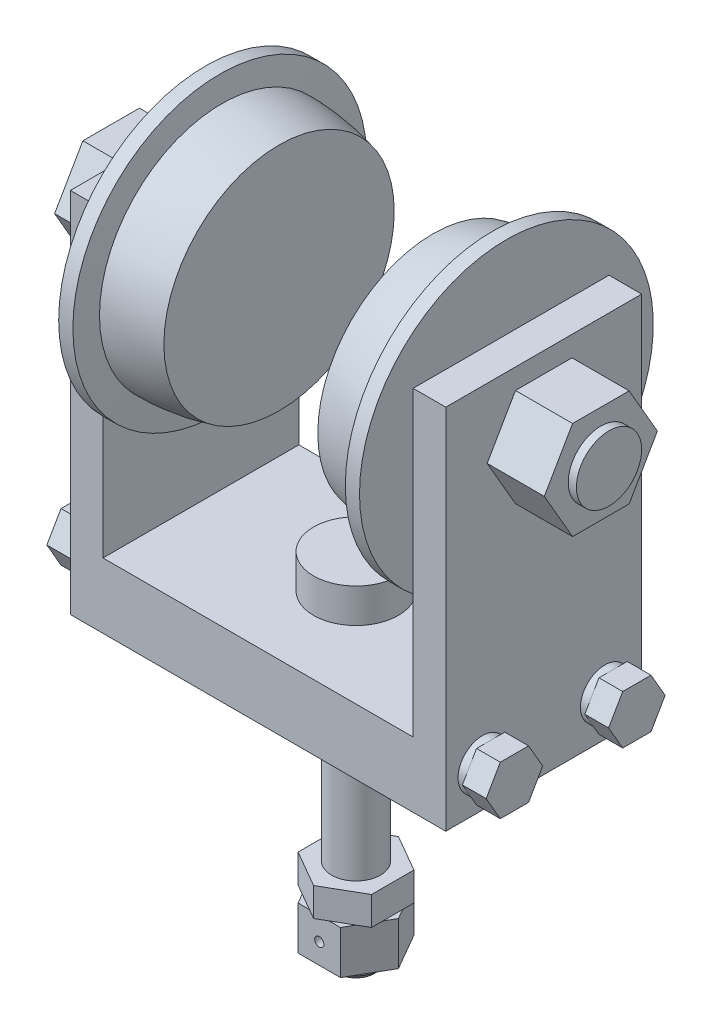
SolidWorks part; units mm, degrees
ref_plane "Front" through (0, 0, 0) normal (0, 0, 1) x (1, 0, 0)
ref_plane "Top" through (0, 0, 0) normal (0, 1, 0) x (1, 0, 0)
ref_plane "Right" through (0, 0, 0) normal (1, 0, 0) x (0, 0, -1)
ref_plane "Z PLANE" through (0, 0, 0) normal (0, 0, 1) x (1, 0, 0)
ref_plane "YOKE BOTTOM" through (0, 0, 0) normal (0, 1, 0) x (-1, 0, 0)
ref_plane "X PLANE" through (0, 0, 0) normal (1, 0, 0) x (0, 0, -1)
sketch "YOKE CROSS SECTION" plane through (0, 0, 0) normal (1, 0, 0) x (0, 0, -1)
  line L0 (0, 0) -> (0, 57.0916) construction
  line L1 (0, 72.125) -> (0, -72.125) construction
  line L2 (-38.1, 0) -> (38.1, 0)
  line L3 (69.1602, 0) -> (-69.1602, 0) construction
  line L4 (38.1, 0) -> (38.1, 25.4)
  line L5 (-38.1, 0) -> (-38.1, 25.4)
  line L6 (38.1, 25.4) -> (-38.1, 25.4)
  point P12 (0, 25.4)
  dimension "D1" = 25.4
  dimension "D2" = 76.2
ref_plane "1/2 YOKE LENGTH (A)" through (60.325, 0, 0) normal (1, 0, 0) x (0, 0, -1)
extrude "YOKE" add sketch "YOKE CROSS SECTION" along normal up to surface (60.325 mm away) up to plane "1/2 YOKE LENGTH (A)"
sketch "SIDEPLATE PROFILE" plane through (60.325, 0, 0) normal (1, 0, 0) x (0, 0, -1)
  line L0 (0, 0) -> (0, 74.7424) construction
  line L1 (0, 72.125) -> (0, -72.125) construction
  line L2 (-38.1, 0) -> (38.1, 0)
  line L3 (38.1, 0) -> (38.1, 142.875)
  line L4 (-38.1, 0) -> (-38.1, 142.875)
  line L5 (38.1, 142.875) -> (-38.1, 142.875)
  point P11 (0, 142.875)
  dimension "D1" = 142.875
ref_plane "WHEEL HEIGHT" through (0, 115.8875, 0) normal (0, 1, 0) x (-1, 0, 0)
ref_plane "SCREW LOCATION X" through (0, 0, 23.8125) normal (0, 0, 1) x (1, 0, 0)
ref_plane "SCREW LOCATION Y" through (0, 15.5632, 0) normal (0, 1, 0) x (-1, 0, 0)
extrude "SIDEPLATE" add sketch "SIDEPLATE PROFILE" along normal blind 12.7
sketch "WHEEL PIN NUT PROFILE" plane through (73.025, 0, 0) normal (1, 0, 0) x (0, 0, -1)
  line L0 (0, 72.125) -> (0, -72.125) construction
  line L1 (21.997, 115.8875) -> (10.9985, 134.9375)
  line L2 (10.9985, 134.9375) -> (-10.9985, 134.9375)
  line L3 (-10.9985, 134.9375) -> (-21.997, 115.8875)
  line L4 (-21.997, 115.8875) -> (-10.9985, 96.8375)
  line L5 (-10.9985, 96.8375) -> (10.9985, 96.8375)
  line L6 (10.9985, 96.8375) -> (21.997, 115.8875)
  line L7 (69.1602, 115.8875) -> (-69.1602, 115.8875) construction
  circle A0 centre (0, 115.8875) radius 19.05 construction
  dimension "D1" = 38.1
extrude "WHEEL PIN NUT" add sketch "WHEEL PIN NUT PROFILE" along normal blind 22.225
sketch "WHEEL PIN PROJECTION PROFILE" plane through (95.25, 0, 0) normal (1, 0, 0) x (0, 0, -1)
  line L0 (0, 72.125) -> (0, -72.125) construction
  line L1 (69.1602, 115.8875) -> (-69.1602, 115.8875) construction
  circle A0 centre (0, 115.8875) radius 12.7
  dimension "D1" = 25.4
extrude "WHEEL PIN PROJECTION" add sketch "WHEEL PIN PROJECTION PROFILE" along normal blind 3.175
sketch "LOCKNUTS PROFILE" plane through (73.025, 0, 0) normal (1, 0, 0) x (0, 0, -1)
  line L0 (-23.8125, 84.8167) -> (-23.8125, -84.8167) construction
  line L1 (50, 15.5632) -> (-50, 15.5632) construction
  circle A0 centre (-23.8125, 15.5632) radius 9.525
  dimension "D1" = 19.05
extrude "LOCKNUTS" add sketch "LOCKNUTS PROFILE" along normal blind 3.175
sketch "SCREWS PROFILE" plane through (76.2, 0, 0) normal (1, 0, 0) x (0, 0, -1)
  line L0 (50, 15.5632) -> (-50, 15.5632) construction
  line L1 (-12.814, 15.5632) -> (-18.3132, 25.0882)
  line L2 (-18.3132, 25.0882) -> (-29.3118, 25.0882)
  line L3 (-29.3118, 25.0882) -> (-34.811, 15.5632)
  line L4 (-34.811, 15.5632) -> (-29.3118, 6.0382)
  line L5 (-29.3118, 6.0382) -> (-18.3132, 6.0382)
  line L6 (-18.3132, 6.0382) -> (-12.814, 15.5632)
  line L7 (-23.8125, 84.8167) -> (-23.8125, -84.8167) construction
  circle A0 centre (-23.8125, 15.5632) radius 9.525 construction
  dimension "D1" = 19.05
extrude "SCREWS" add sketch "SCREWS PROFILE" along normal blind 9.2456
sketch "PROFILE" plane through (0, 25.4, 0) normal (0, 1, 0) x (-1, 0, 0)
  line L0 (72.125, 0) -> (-72.125, 0) construction
  line L1 (0, 83.2389) -> (0, -83.2389) construction
  circle A0 centre (0, 0) radius 16.4973
  dimension "D1" = 32.9946
extrude "KING BOLT HEAD" add sketch "PROFILE" along normal blind 13.3096
mirror "Mirror1" about plane through (0, 0, 0) normal (0, 0, 1) of "SCREWS", "LOCKNUTS"
mirror "Mirror5" about plane through (0, 0, 0) normal (1, 0, 0) of bodies 112
ref_plane "TOP OF NUT" through (0, -65.5896, 0) normal (0, 1, 0) x (-1, 0, 0)
sketch "DIA." plane through (0, 0, 0) normal (0, -1, 0) x (1, 0, 0)
  line L0 (72.125, 0) -> (-72.125, 0) construction
  line L1 (0, -83.2389) -> (0, 83.2389) construction
  circle A0 centre (0, 0) radius 9.525
  dimension "D1" = 19.05
extrude "KING BOLT" add sketch "DIA." along normal up to surface (65.5896 mm away) up to plane "TOP OF NUT"
sketch "KING BOLT JAN NUT PROFILE" plane through (0, -65.5896, 0) normal (0, -1, 0) x (1, 0, 0)
  line L0 (72.125, 0) -> (-72.125, 0) construction
  line L1 (0, -16.4978) -> (14.2875, -8.2489)
  line L2 (14.2875, -8.2489) -> (14.2875, 8.2489)
  line L3 (14.2875, 8.2489) -> (0, 16.4978)
  line L4 (0, 16.4978) -> (-14.2875, 8.2489)
  line L5 (-14.2875, 8.2489) -> (-14.2875, -8.2489)
  line L6 (-14.2875, -8.2489) -> (0, -16.4978)
  line L7 (0, -83.2389) -> (0, 83.2389) construction
  circle A0 centre (0, 0) radius 14.2875 construction
  dimension "D1" = 28.575
extrude "KING BOLT JAM NUT" add sketch "KING BOLT JAN NUT PROFILE" along normal blind 11.1125
sketch "KING BOLT NUT PROFILE" plane through (0, -76.7021, 0) normal (0, -1, 0) x (1, 0, 0)
  line L1 (16.4978, 0) -> (8.2489, 14.2875)
  line L2 (8.2489, 14.2875) -> (-8.2489, 14.2875)
  line L3 (-8.2489, 14.2875) -> (-16.4978, 0)
  line L4 (-16.4978, 0) -> (-8.2489, -14.2875)
  line L5 (-8.2489, -14.2875) -> (8.2489, -14.2875)
  line L6 (8.2489, -14.2875) -> (16.4978, 0)
  line L10 (0, -83.2389) -> (0, 83.2389) construction
  line L11 (72.125, 0) -> (-72.125, 0) construction
  circle A0 centre (0, 0) radius 14.2875 construction
  dimension "D1" = 28.575
extrude "KING BOLT NUT" add sketch "KING BOLT NUT PROFILE" along normal blind 16.891
sketch "Sketch5" plane through (0, -93.5931, 0) normal (0, -1, 0) x (1, 0, 0)
  circle A0 centre (0, 0) radius 9.525 construction
  circle A1 centre (0, 0) radius 9.525
extrude "EXTENDED KING BOLT" add sketch "Sketch5" along normal blind 6.35
chamfer "Chamfer1" distance 2.3812 angle 45 1 edges at (0, -99.9431, -9.525)
ref_plane "MOUNTING REF PLANE" through (0, -34.925, 0) normal (0, 1, 0) x (-1, 0, 0)
sketch "Sketch7" plane through (0, 0, 0) normal (0, 0, 1) x (1, 0, 0)
  line L0 (29.9333, 160.6896) -> (29.9333, 115.8875)
  line L1 (60.325, 115.8875) -> (60.325, 131.7625)
  line L2 (29.9333, 115.8875) -> (60.325, 115.8875)
  line L3 (58.5083, 131.7625) -> (58.5083, 173.0375)
  line L4 (60.325, 131.7625) -> (58.5083, 131.7625)
  line L5 (52.9916, 173.0375) -> (52.1583, 163.5125)
  line L6 (58.5083, 173.0375) -> (52.9916, 173.0375)
  line L7 (69.1602, 115.8875) -> (-69.1602, 115.8875) construction
  line L8 (60.325, 142.875) -> (60.325, 25.4) construction
  arc A0 (52.1583, 163.5125) -> (29.9333, 160.6896) centre (52.1583, 74.6125) ccw
  dimension "D1" = 88.9
  dimension "D2" = 30.3917
  dimension "D6" = 1.8167
  dimension "D3" = 8.1667
  dimension "D4" = 8.1667
  dimension "D5" = 41.275
  dimension "D7" = 5.5167
  dimension "D8" = 57.15
  dimension "D9" = 15.875
revolve "WHEEL" add sketch "Sketch7" angle 360 about L2
mirror "Mirror6" about plane through (0, 0, 0) normal (1, 0, 0) of "WHEEL"
sketch "Sketch8" plane through (0, 0, 14.2875) normal (0, 0, 1) x (1, 0, 0)
  line L0 (0, -83.2389) -> (0, 83.2389) construction
  line L1 (8.2489, -93.5931) -> (-8.2489, -93.5931) construction
  circle A0 centre (0, -85.6556) radius 1.778
  dimension "D1" = 3.556
  dimension "D2" = 7.9375
extrude "COTTER PIN HOLE" cut sketch "Sketch8" against normal up to next
sketch "Sketch9" plane through (0, 0, 0) normal (0, -1, 0) x (1, 0, 0)
  circle A0 centre (0, 0) radius 25.4
  circle A1 centre (0, 0) radius 30.1625
  dimension "D1" = 50.8
  dimension "D2" = 60.325
extrude "SPACER" [suppressed] add sketch "Sketch9" along normal blind 12.7
ref_plane "TREAD OF TRACK" through (0, 68.2625, 0) normal (0, 1, 0) x (-1, 0, 0)
